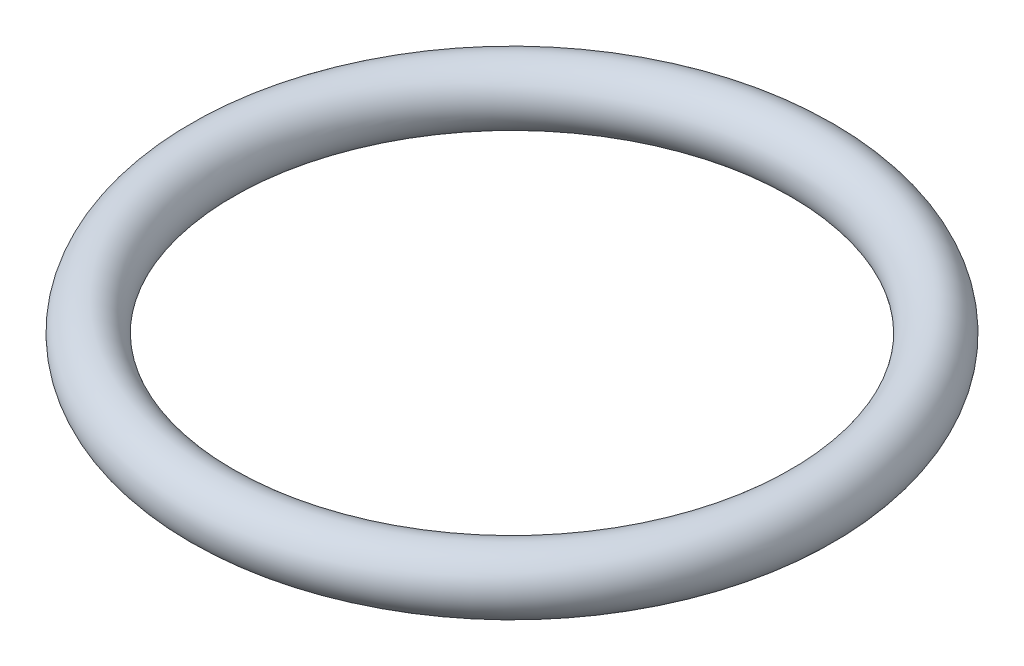
SolidWorks part; units mm, degrees
ref_plane "Front" through (0, 0, 0) normal (0, 0, 1) x (1, 0, 0)
ref_plane "Top" through (0, 0, 0) normal (0, 1, 0) x (1, 0, 0)
ref_plane "Right" through (0, 0, 0) normal (1, 0, 0) x (0, 0, -1)
sketch "Support-Top" plane through (0, 0, 0) normal (0, 1, 0) x (1, 0, 0)
  line L0 (0, 0) -> (0, 16) construction
  line L1 (-16, 16) -> (16, 16) construction
  line L2 (-16, 16) -> (-16, -16) construction
  line L3 (-16, -16) -> (16, -16) construction
  line L4 (16, 16) -> (16, -16) construction
  line L5 (0, 0) -> (16, 0) construction
  line L6 (16, 16) -> (0, 8.5391) construction
  circle A0 centre (0, 0) radius 8.5391
  point P9 (8.5391, 0)
  dimension "D1" = 32
  dimension "D2" = 32
  dimension "D3" = 25
sketch "Support-Front" plane through (0, 0, 0) normal (0, 0, 1) x (1, 0, 0)
  line L0 (8.5391, 0) -> (-8.5391, 0) construction
  line L1 (8.5391, 0) -> (8.5391, 0.85) construction
  circle A0 centre (8.5391, 0) radius 0.85
  dimension "D1" = 1.7
sketch "Sketch3" plane through (0, 0, 0) normal (0, 1, 0) x (1, 0, 0)
  circle A0 centre (0, 0) radius 8.5391 construction
  circle A1 centre (0, 0) radius 8.5391
sketch "Sketch4" plane through (0, 0, 0) normal (0, 0, 1) x (1, 0, 0)
  circle A0 centre (8.5391, 0) radius 0.85 construction
  circle A1 centre (8.5391, 0) radius 0.85
ref_plane "Ref-Plane" through (0, 0.85, 0) normal (0, 1, 0) x (-1, 0, 0)
sweep "Body" add profiles "Sketch4" path "Sketch3"
